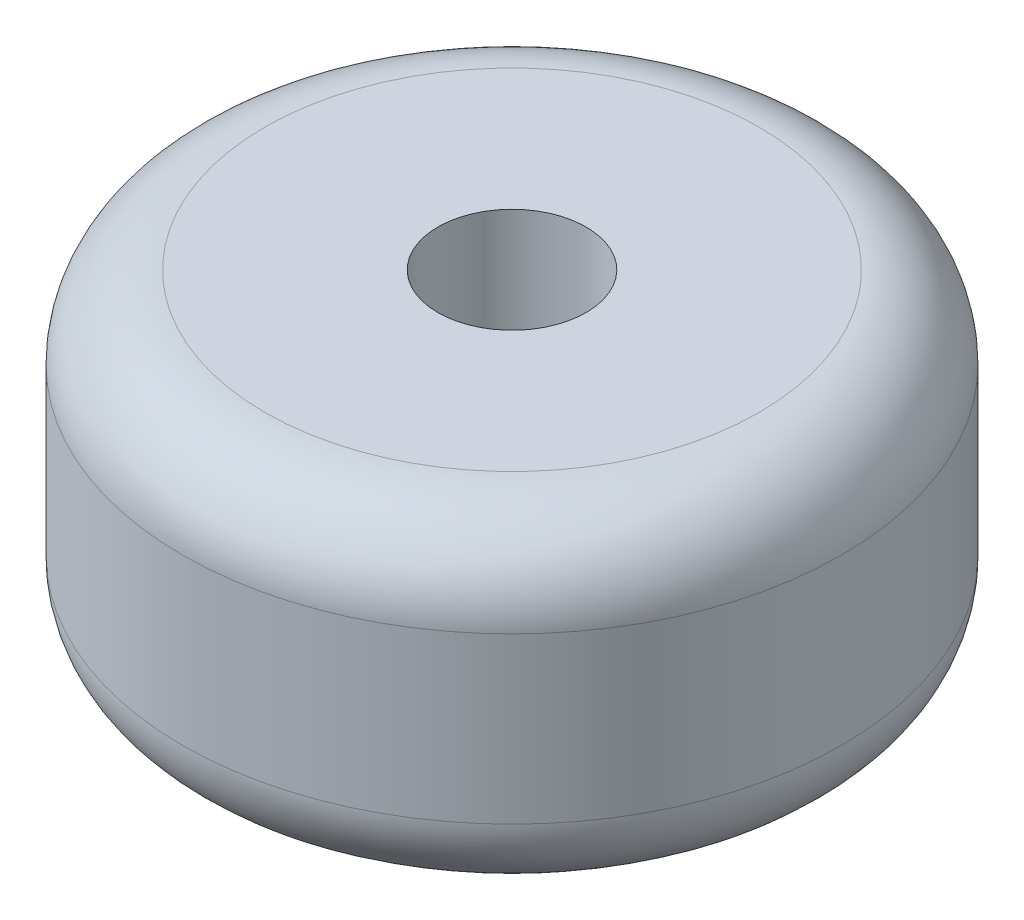
SolidWorks part; units mm, degrees
ref_plane "Front" through (0, 0, 0) normal (0, 0, 1) x (1, 0, 0)
ref_plane "Top" through (0, 0, 0) normal (0, 1, 0) x (1, 0, 0)
ref_plane "Right" through (0, 0, 0) normal (1, 0, 0) x (0, 0, -1)
sketch "草图1" plane through (0, 0, 0) normal (0, 1, 0) x (1, 0, 0)
  circle A0 centre (0, 0) radius 2
  dimension "D1" = 4
extrude "凸台-拉伸1" add sketch "草图1" along normal blind 2
sketch "草图2" plane through (0, 2, 0) normal (0, 1, 0) x (1, 0, 0)
  circle A0 centre (0, 0) radius 0.45
  dimension "D1" = 0.9
extrude "切除-拉伸1" cut sketch "草图2" against normal through all
fillet "圆角1" radius 0.5 2 edges at (0, 0, 2) (0, 2, 2)
